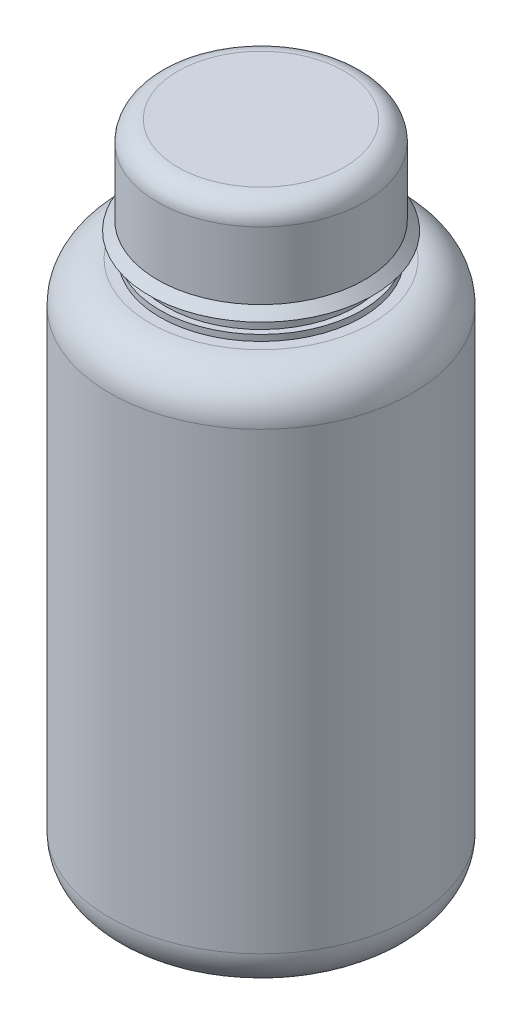
SolidWorks part; units mm, degrees
material "PE High Density"
ref_plane "Front Plane" through (0, 0, 0) normal (0, 0, 1) x (1, 0, 0)
ref_plane "Top Plane" through (0, 0, 0) normal (0, 1, 0) x (1, 0, 0)
ref_plane "Right Plane" through (0, 0, 0) normal (1, 0, 0) x (0, 0, -1)
sketch "Sketch1" plane through (0, 0, 0) normal (0, 1, 0) x (1, 0, 0)
  line L1 (-41.275, 47.625) -> (41.275, 47.625)
  line L2 (-47.625, 41.275) -> (-47.625, -41.275)
  line L3 (-41.275, -47.625) -> (41.275, -47.625)
  line L4 (47.625, 41.275) -> (47.625, -41.275)
  line L5 (-47.625, 47.625) -> (47.625, -47.625) construction
  line L6 (-47.625, -47.625) -> (47.625, 47.625) construction
  arc A0 (-47.625, -41.275) -> (-41.275, -47.625) centre (-41.275, -41.275) ccw
  arc A1 (41.275, -47.625) -> (47.625, -41.275) centre (41.275, -41.275) ccw
  arc A2 (41.275, 47.625) -> (47.625, 41.275) centre (41.275, 41.275) cw
  arc A3 (-41.275, 47.625) -> (-47.625, 41.275) centre (-41.275, 41.275) ccw
  point P0 (0, 0)
  dimension "D2" = 6.35
  dimension "D1" = 95.25
extrude "Boss-Extrude1" [suppressed] add sketch "Sketch1" along normal blind 219.075
sketch "Sketch3" [suppressed] plane through (0, 0, 0) normal (1, 0, 0) x (0, 0, -1)
  line L0 (-19.05, 219.075) -> (-19.05, 189.3151)
  line L1 (-41.275, 219.075) -> (41.275, 219.075) construction
  line L2 (-19.05, 189.3151) -> (-14.2784, 189.3151)
  line L3 (-14.2784, 189.3151) -> (-14.2784, 186.7159)
  line L4 (-14.2784, 186.7159) -> (-18.4051, 186.7159)
  line L5 (-18.4051, 186.7159) -> (-98.1999, 100.9425)
  line L6 (-98.1999, 100.9425) -> (-98.1999, 234.3521)
  line L7 (-98.1999, 234.3521) -> (-19.05, 234.3521)
  line L8 (-19.05, 234.3521) -> (-19.05, 219.075)
  line L9 (0, -58.4474) -> (0, 397.1255) construction
  dimension "D1" = 38.1
revolve "Cut-Revolve1" [suppressed] cut sketch "Sketch3" angle 360 about L9
fillet "Fillet3" [suppressed] radius 3.175
fillet "Fillet4" [suppressed] radius 12.7
sketch "Sketch4" plane through (0, 0, 0) normal (1, 0, 0) x (0, 0, -1)
  line L0 (0, -30.5347) -> (0, 29.6232) construction
  line L1 (0, 0) -> (-34.925, 0)
  line L2 (-47.625, 12.7) -> (-47.625, 155.575)
  line L3 (-34.925, 168.275) -> (-31.75, 168.275)
  line L4 (-31.75, 168.275) -> (-31.75, 170.1884)
  line L5 (-31.75, 170.1884) -> (-29.8508, 170.1884)
  line L6 (-29.8508, 170.1884) -> (-29.8508, 174.1135)
  line L7 (-29.8508, 174.1135) -> (-31.75, 174.1135)
  line L8 (-31.75, 174.1135) -> (-31.75, 176.0154)
  line L9 (-31.75, 176.0154) -> (-35.2591, 176.0154)
  line L10 (-35.2591, 176.0154) -> (-32.5437, 178.8703)
  line L11 (-32.5437, 178.8703) -> (-32.5437, 200.025)
  line L12 (-26.1937, 206.375) -> (0, 206.375)
  line L13 (0, 0) -> (0, 206.375)
  arc A0 (-34.925, 0) -> (-47.625, 12.7) centre (-34.925, 12.7) cw
  arc A1 (-47.625, 155.575) -> (-34.925, 168.275) centre (-34.925, 155.575) cw
  arc A2 (-32.5437, 200.025) -> (-26.1937, 206.375) centre (-26.1937, 200.025) cw
  point P6 (-35.408, 176.1906)
  point P17 (-32.5316, 178.8703)
  point P18 (-35.2591, 176.0154)
  dimension "D5" = 12.7
  dimension "D6" = 6.35
  dimension "D1" = 95.25
  dimension "D2" = 206.375
  dimension "D3" = 63.5
  dimension "D4" = 65.0875
  dimension "D7" = 142.875
revolve "Revolve1" add sketch "Sketch4" angle 360 about L0
